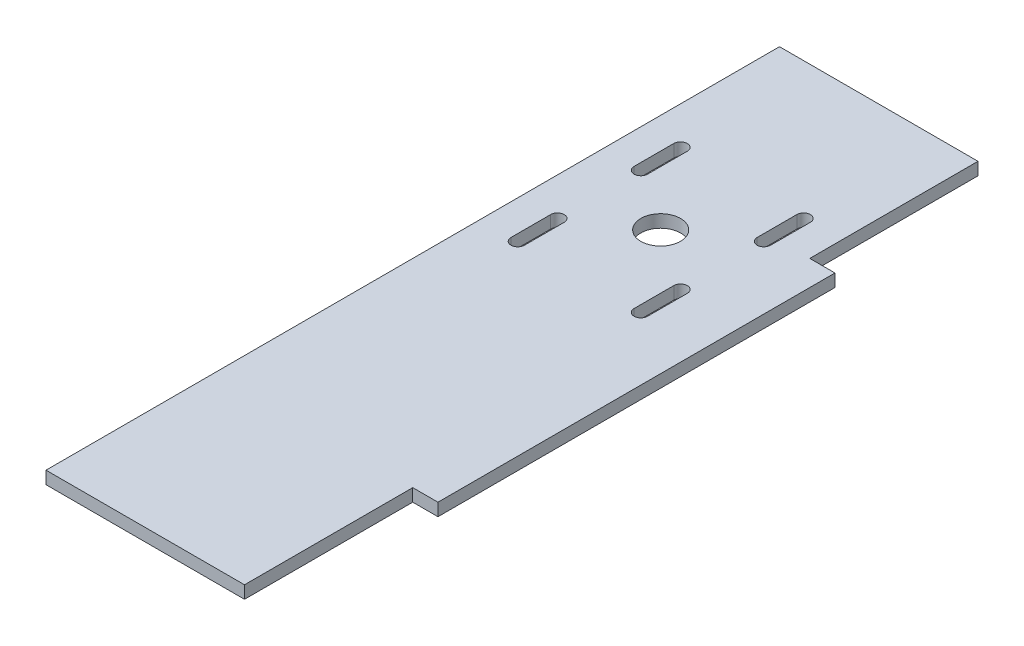
SolidWorks part; units mm, degrees
ref_plane "Front Plane" through (0, 0, 0) normal (0, 0, 1) x (1, 0, 0)
ref_plane "Top Plane" through (0, 0, 0) normal (0, 1, 0) x (1, 0, 0)
ref_plane "Right Plane" through (0, 0, 0) normal (1, 0, 0) x (0, 0, -1)
sketch "Sketch1" plane through (0, 0, 0) normal (0, 1, 0) x (1, 0, 0)
  line L0 (-25, 42.375) -> (25, 42.375)
  line L1 (25, 42.375) -> (25, 0)
  line L2 (25, 0) -> (31.35, 0)
  line L3 (31.35, 0) -> (31.35, -100)
  line L4 (31.35, -100) -> (25, -100)
  line L5 (25, -100) -> (25, -142.375)
  line L6 (25, -142.375) -> (-25, -142.375)
  line L7 (-25, -142.375) -> (-25, -100)
  line L8 (-25, -100) -> (-31.35, -100)
  line L9 (-31.35, -100) -> (-31.35, 0)
  line L10 (-31.35, 0) -> (-25, 0)
  line L11 (-25, 0) -> (-25, 42.375)
  line L12 (-25, 0) -> (-25, -100) construction
  point P11 (0, 42.375)
  point P14 (-31.35, -50)
  dimension "D1" = 6.35
  dimension "D2" = 100
  dimension "D3" = 50
  dimension "D4" = 184.75
extrude "Boss-Extrude1" add sketch "Sketch1" along normal blind 3.175 contours L11 L12 L7 L6 L5 L4 L3 L2 L1 L0
sketch "Sketch2" plane through (0, 3.175, 0) normal (0, 1, 0) x (1, 0, 0)
  line L1 (25, 12.45) -> (-25, 12.45) construction
  line L2 (25, 12.45) -> (25, -37.55) construction
  line L3 (25, -37.55) -> (-25, -37.55) construction
  line L4 (-25, 12.45) -> (-25, -37.55) construction
  line L5 (0, 11.95) -> (0, -37.05) construction
  line L6 (-15.5, 2.95) -> (15.5, 2.95) construction
  line L7 (15.5, 2.95) -> (15.5, -28.05) construction
  line L8 (25, -142.375) -> (-25, -142.375) construction
  circle A0 centre (0, -12.55) radius 5
  point P5 (0, -37.55)
  point P8 (0, -142.375)
  point P9 (0, 11.95)
  point P10 (0, -37.05)
  point P13 (25, -12.55)
  point P14 (0, -12.55)
  point P15 (15.5, 2.95)
  point P16 (-15.5, 2.95)
  point P17 (15.5, -28.05)
  point P18 (-15.5, -28.05)
  point P21 (0, 2.95)
  point P22 (15.5, -12.55)
  dimension "D6" = 10
  dimension "D2" = 50
  dimension "D5" = 49
  dimension "D3" = 31
  dimension "D1" = 129.825
extrude "Cut-Extrude1" cut sketch "Sketch2" against normal through all
hole_wizard "M3 Clearance Hole1" positions "Sketch6" profile "Sketch5" hole size "M3" standard "ANSI Metric" end condition through all
sketch "Sketch6" plane through (0, 3.175, 0) normal (0, 1, 0) x (1, 0, 0)
  point P6 (-15.5, 2.95)
  point P9 (15.5, 2.95)
  point P12 (15.5, -28.05)
  point P15 (-15.5, -28.05)
sketch "Sketch5" plane through (-15.5, 3.175, -2.95) normal (1, 0, 0) x (0, 0, 1)
  line L0 (0, 0) -> (0, 3.175)
  line L1 (0, 3.175) -> (1.7, 3.175)
  line L2 (1.7, 3.175) -> (1.7, 0)
  line L5 (1.7, 0) -> (0, 0)
  line L11 (0, -6.35) -> (0, 107.95) construction
  dimension "Thru Hole Dia." = 3.4
  dimension "Thru Hole Depth" = 3.175
sketch "Sketch7" plane through (0, 3.175, 0) normal (0, 1, 0) x (1, 0, 0)
  line L0 (15.5, 7.95) -> (15.5, -2.05) construction
  line L1 (17.2, 7.95) -> (17.2, -2.05)
  line L2 (13.8, 7.95) -> (13.8, -2.05)
  line L3 (-15.5, 7.95) -> (-15.5, -2.05) construction
  line L4 (-13.8, 7.95) -> (-13.8, -2.05)
  line L5 (-17.2, 7.95) -> (-17.2, -2.05)
  line L6 (21.8073, -12.55) -> (-21.8073, -12.55) construction
  line L7 (15.5, -33.05) -> (15.5, -23.05) construction
  line L8 (17.2, -33.05) -> (17.2, -23.05)
  line L9 (13.8, -33.05) -> (13.8, -23.05)
  line L10 (-15.5, -33.05) -> (-15.5, -23.05) construction
  line L11 (-13.8, -33.05) -> (-13.8, -23.05)
  line L12 (-17.2, -33.05) -> (-17.2, -23.05)
  arc A0 (17.2, 7.95) -> (13.8, 7.95) centre (15.5, 7.95) ccw
  arc A1 (13.8, -2.05) -> (17.2, -2.05) centre (15.5, -2.05) ccw
  arc A2 (-13.8, 7.95) -> (-17.2, 7.95) centre (-15.5, 7.95) ccw
  arc A3 (-17.2, -2.05) -> (-13.8, -2.05) centre (-15.5, -2.05) ccw
  circle A4 centre (-15.5, 2.95) radius 1.7 construction
  circle A5 centre (15.5, 2.95) radius 1.7 construction
  circle A6 centre (0, -12.55) radius 5 construction
  arc A7 (17.2, -33.05) -> (13.8, -33.05) centre (15.5, -33.05) cw
  arc A8 (13.8, -23.05) -> (17.2, -23.05) centre (15.5, -23.05) cw
  arc A9 (-13.8, -33.05) -> (-17.2, -33.05) centre (-15.5, -33.05) cw
  arc A10 (-17.2, -23.05) -> (-13.8, -23.05) centre (-15.5, -23.05) cw
  point P2 (15.5, 2.95)
  point P9 (-15.5, 2.95)
  point P22 (0, -12.55)
  point P27 (15.5, -28.05)
  point P34 (-15.5, -28.05)
  dimension "D1" = 10
extrude "Cut-Extrude2" cut sketch "Sketch7" against normal through all
sketch "Sketch8" plane through (0, 3.175, 0) normal (0, 1, 0) x (1, 0, 0)
  line L8 (-25, 42.375) -> (-25, -142.375)
  line L9 (-25, -142.375) -> (25, -142.375)
  line L10 (25, -142.375) -> (25, -100)
  line L11 (25, -100) -> (31.35, -100)
  line L12 (31.35, -100) -> (31.35, 0)
  line L13 (31.35, 0) -> (25, 0)
  line L14 (25, 0) -> (25, 42.375)
  line L15 (25, 42.375) -> (-25, 42.375)
  line L16 (-25, 42.375) -> (-25, -142.375)
  line L17 (-25, -142.375) -> (25, -142.375)
  line L18 (25, -142.375) -> (25, -100)
  line L19 (25, -100) -> (31.35, -100)
  line L20 (31.35, -100) -> (31.35, 0)
  line L21 (31.35, 0) -> (25, 0)
  line L22 (25, 0) -> (25, 42.375)
  line L23 (25, 42.375) -> (-25, 42.375)
  line L32 (13.8, 7.95) -> (13.8, -2.05) construction
  line L33 (17.2, -2.05) -> (17.2, 7.95) construction
  line L34 (-13.8, -2.05) -> (-13.8, 7.95) construction
  line L35 (-17.2, 7.95) -> (-17.2, -2.05) construction
  line L36 (-17.2, -23.05) -> (-17.2, -33.05) construction
  line L37 (-13.8, -33.05) -> (-13.8, -23.05) construction
  line L38 (13.8, -23.05) -> (13.8, -33.05) construction
  line L39 (17.2, -33.05) -> (17.2, -23.05) construction
  line L40 (13.8, 7.95) -> (13.8, -2.05)
  line L41 (17.2, -2.05) -> (17.2, 7.95)
  line L42 (-13.8, -2.05) -> (-13.8, 7.95)
  line L43 (-17.2, 7.95) -> (-17.2, -2.05)
  line L44 (-17.2, -23.05) -> (-17.2, -33.05)
  line L45 (-13.8, -33.05) -> (-13.8, -23.05)
  line L46 (13.8, -23.05) -> (13.8, -33.05)
  line L47 (17.2, -33.05) -> (17.2, -23.05)
  arc A0 (17.2, 7.95) -> (13.8, 7.95) centre (15.5, 7.95) ccw construction
  arc A1 (13.8, -2.05) -> (17.2, -2.05) centre (15.5, -2.05) ccw construction
  arc A2 (-13.8, 7.95) -> (-17.2, 7.95) centre (-15.5, 7.95) ccw construction
  arc A3 (-17.2, -2.05) -> (-13.8, -2.05) centre (-15.5, -2.05) ccw construction
  arc A4 (-13.8, -23.05) -> (-17.2, -23.05) centre (-15.5, -23.05) ccw construction
  arc A5 (-17.2, -33.05) -> (-13.8, -33.05) centre (-15.5, -33.05) ccw construction
  circle A6 centre (0, -12.55) radius 5 construction
  arc A7 (17.2, -23.05) -> (13.8, -23.05) centre (15.5, -23.05) ccw construction
  arc A8 (13.8, -33.05) -> (17.2, -33.05) centre (15.5, -33.05) ccw construction
  arc A9 (17.2, 7.95) -> (13.8, 7.95) centre (15.5, 7.95) ccw
  arc A10 (13.8, -2.05) -> (17.2, -2.05) centre (15.5, -2.05) ccw
  arc A11 (-13.8, 7.95) -> (-17.2, 7.95) centre (-15.5, 7.95) ccw
  arc A12 (-17.2, -2.05) -> (-13.8, -2.05) centre (-15.5, -2.05) ccw
  arc A13 (-13.8, -23.05) -> (-17.2, -23.05) centre (-15.5, -23.05) ccw
  arc A14 (-17.2, -33.05) -> (-13.8, -33.05) centre (-15.5, -33.05) ccw
  circle A15 centre (0, -12.55) radius 5
  arc A16 (17.2, -23.05) -> (13.8, -23.05) centre (15.5, -23.05) ccw
  arc A17 (13.8, -33.05) -> (17.2, -33.05) centre (15.5, -33.05) ccw
  dimension "D1" = 0
equation "\"length\"= 184.75mm"
equation "\"w_mach\"= 60mm"
equation "\"w_tab\"= 100mm"
equation "\"t_wood\"= 0.125in"
equation "\"t_side\"= 0.25in"
equation "\"D1@Sketch1\"=\"t_side\""
equation "\"D2@Sketch1\"=\"w_tab\""
equation "\"D3@Sketch1\"=\"l_motor\""
equation "\"D4@Sketch1\"=\"length\""
equation "\"D1@Boss-Extrude1\"=\"t_wood\""
equation "\"dX\"= 144.825mm"
equation "\"in_rad\"= 15mm"
equation "\"D1@Sketch2\"=\"dX\"-\"in_rad\""
equation "\"l_motor\"= 50mm"
equation "\"l_servo\"= 40mm"
equation "\"servocenter\"= 6.35mm"
equation "\"D2@Sketch2\"=\"l_motor\""
equation "\"D3@Sketch2\"=31"
equation "\"servoholes\"= 49mm"
equation "\"D5@Sketch2\"= \"servoholes\""
